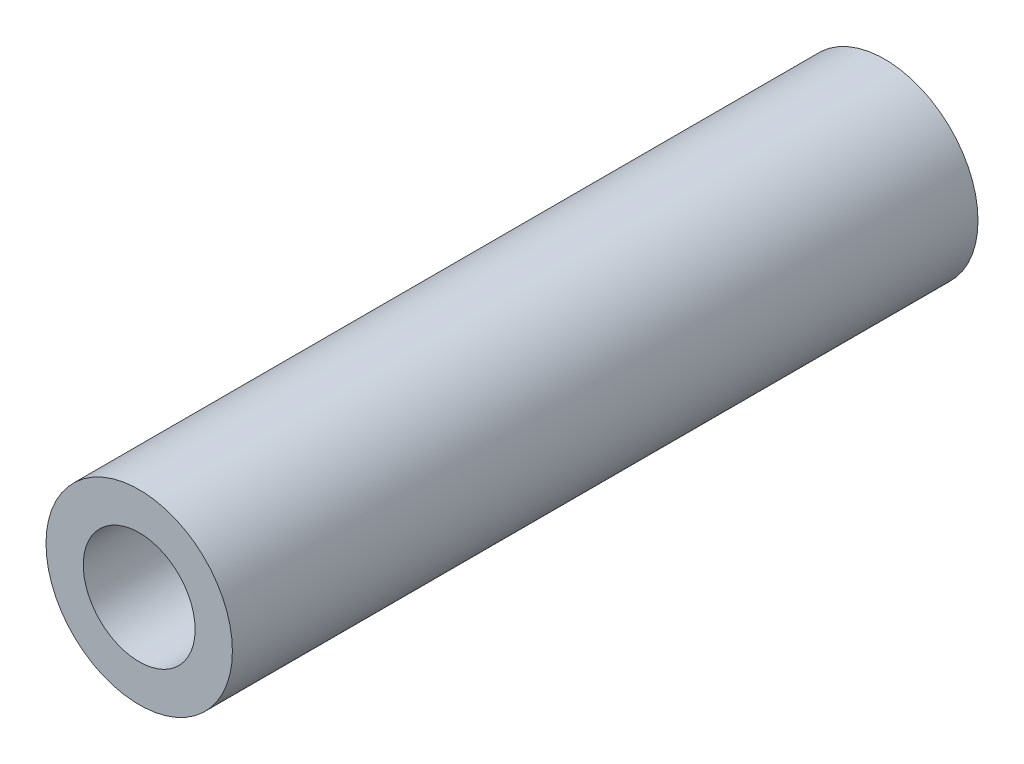
SolidWorks part; units mm, degrees
ref_plane "Front Plane" through (0, 0, 0) normal (0, 0, 1) x (1, 0, 0)
ref_plane "Top Plane" through (0, 0, 0) normal (0, 1, 0) x (1, 0, 0)
ref_plane "Right Plane" through (0, 0, 0) normal (1, 0, 0) x (0, 0, -1)
sketch "Sketch1" plane through (0, 0, 0) normal (0, 0, 1) x (1, 0, 0)
  circle A0 centre (0, 0) radius 2.5
  circle A1 centre (0, 0) radius 1.5
  dimension "D1" = 3
  dimension "D2" = 5
  dimension "D3" = 3
extrude "Boss-Extrude1" add sketch "Sketch1" along normal blind 20
